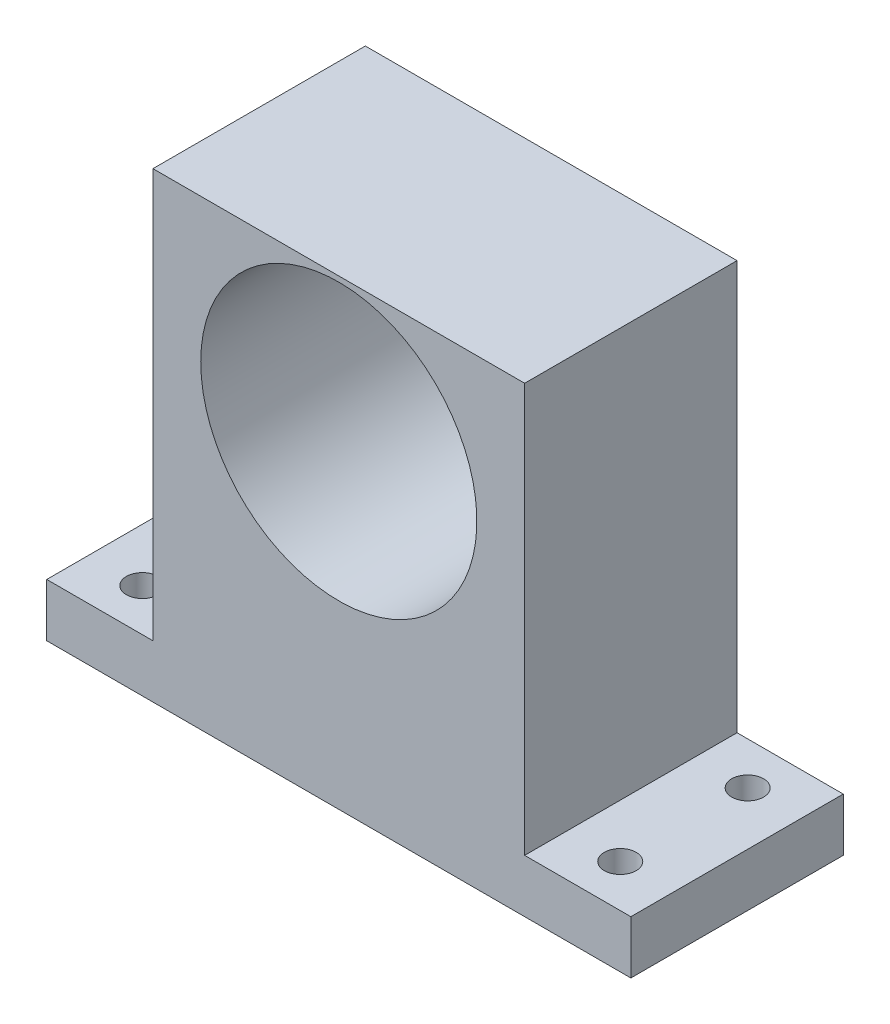
SolidWorks part; units mm, degrees
ref_plane "Спереди" through (0, 0, 0) normal (0, 0, 1) x (1, 0, 0)
ref_plane "Сверху" through (0, 0, 0) normal (0, 1, 0) x (1, 0, 0)
ref_plane "Справа" through (0, 0, 0) normal (1, 0, 0) x (0, 0, -1)
sketch "Эскиз1" plane through (0, 0, 0) normal (0, 0, 1) x (1, 0, 0)
  line L1 (-17.5, -21.75) -> (17.5, -21.75)
  line L2 (-17.5, -21.75) -> (-17.5, 21.75)
  line L3 (-17.5, 21.75) -> (17.5, 21.75)
  line L4 (17.5, -21.75) -> (17.5, 21.75)
  line L5 (-17.5, -21.75) -> (17.5, 21.75) construction
  line L6 (-17.5, 21.75) -> (17.5, -21.75) construction
  point P0 (0, 0)
  dimension "D1" = 35
  dimension "D2" = 43.5
extrude "Бобышка-Вытянуть1" add sketch "Эскиз1" along normal blind 20
sketch "Эскиз2" plane through (17.5, 0, 0) normal (1, 0, 0) x (0, 0, -1)
  line L0 (0, -21.75) -> (0, 21.75) construction
  line L1 (-20, -21.75) -> (0, -21.75)
  line L2 (-20, -21.75) -> (-20, -16.75)
  line L3 (-20, -16.75) -> (0, -16.75)
  line L4 (0, -21.75) -> (0, -16.75)
  dimension "D1" = 5
extrude "Бобышка-Вытянуть2" add sketch "Эскиз2" along normal blind 10
sketch "Эскиз3" plane through (-17.5, 0, 0) normal (-1, 0, 0) x (0, 0, 1)
  line L0 (20, 21.75) -> (20, -21.75) construction
  line L1 (0, -21.75) -> (20, -21.75)
  line L2 (0, -21.75) -> (0, -16.75)
  line L3 (0, -16.75) -> (20, -16.75)
  line L4 (20, -21.75) -> (20, -16.75)
  dimension "D1" = 5
extrude "Бобышка-Вытянуть3" add sketch "Эскиз3" along normal blind 10
sketch "Эскиз4" plane through (0, -16.75, 0) normal (0, 1, 0) x (1, 0, 0)
  line L0 (27.5, 0) -> (27.5, -20) construction
  line L1 (27.5, -20) -> (17.5, -20) construction
  line L2 (27.5, 0) -> (17.5, 0) construction
  line L3 (-27.5, -20) -> (-17.5, -20) construction
  line L4 (-27.5, -20) -> (-27.5, 0) construction
  line L5 (-27.5, 0) -> (-17.5, 0) construction
  circle A0 centre (-22.5, -16) radius 1.5
  circle A1 centre (-22.5, -4) radius 1.5
  circle A2 centre (22.5, -16) radius 1.5
  circle A3 centre (22.5, -4) radius 1.5
  dimension "D1" = 3
  dimension "D2" = 3
  dimension "D3" = 3
  dimension "D4" = 3
  dimension "D5" = 5
  dimension "D6" = 4
  dimension "D7" = 5
  dimension "D8" = 4
  dimension "D9" = 4
  dimension "D10" = 5
  dimension "D11" = 5
  dimension "D12" = 4
extrude "Вырез-Вытянуть2" cut sketch "Эскиз4" against normal blind 5
sketch "Эскиз5" plane through (0, 0, 0) normal (0, 0, -1) x (-1, 0, 0)
  line L0 (27.5, -21.75) -> (-27.5, -21.75) construction
  line L1 (-17.5, -16.75) -> (-17.5, 21.75) construction
  circle A0 centre (0, 8.25) radius 13
  dimension "D1" = 30
  dimension "D2" = 26
  dimension "D3" = 17.5
extrude "Вырез-Вытянуть3" cut sketch "Эскиз5" against normal blind 20
